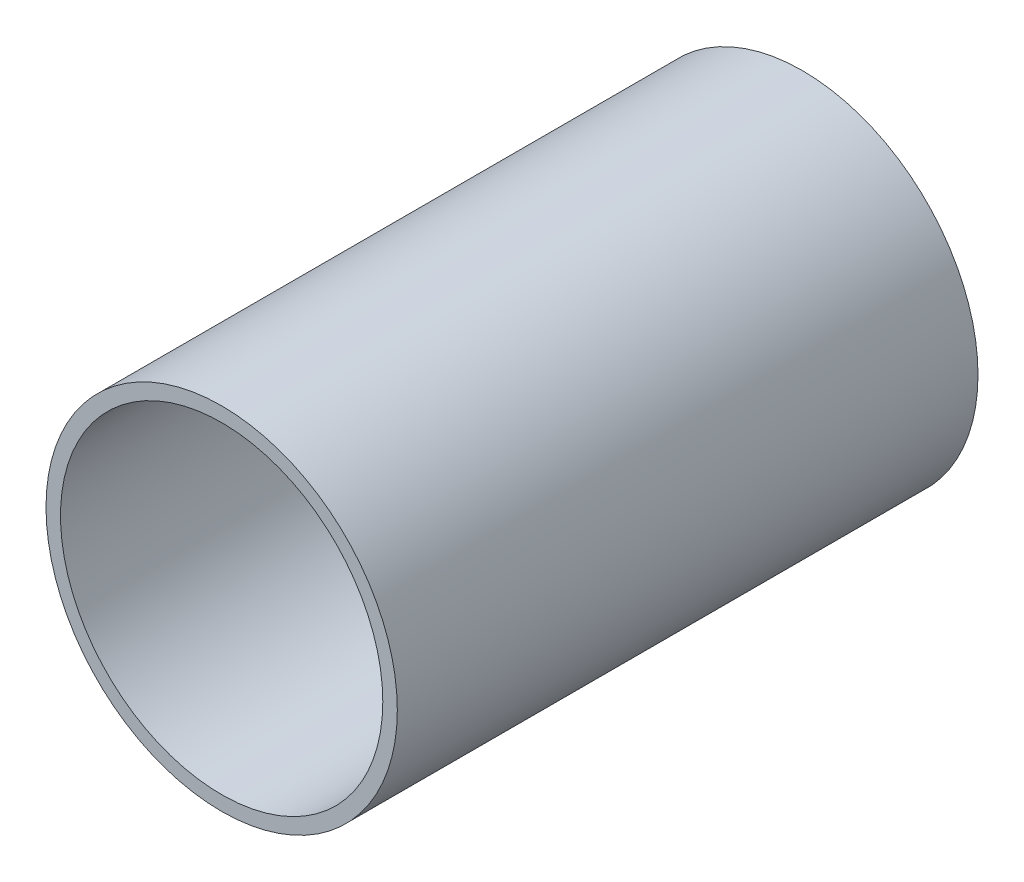
SolidWorks part; units mm, degrees
ref_plane "Front Plane" through (0, 0, 0) normal (0, 0, 1) x (1, 0, 0)
ref_plane "Top Plane" through (0, 0, 0) normal (0, 1, 0) x (1, 0, 0)
ref_plane "Right Plane" through (0, 0, 0) normal (1, 0, 0) x (0, 0, -1)
sketch "Sketch1" plane through (0, 0, 0) normal (1, 0, 0) x (0, 0, -1)
  line L0 (-72.9477, 0) -> (78.5924, 0) construction
  line L2 (-121.4076, 60.5) -> (78.5924, 60.5)
  line L3 (-121.4076, 60.5) -> (-121.4076, 55.5)
  line L4 (-121.4076, 55.5) -> (78.5924, 55.5)
  line L5 (78.5924, 60.5) -> (78.5924, 55.5)
  dimension "D1" = 55.5
  dimension "D2" = 5
  dimension "D3" = 200
revolve "Revolve1" add sketch "Sketch1" angle 360 about L0
